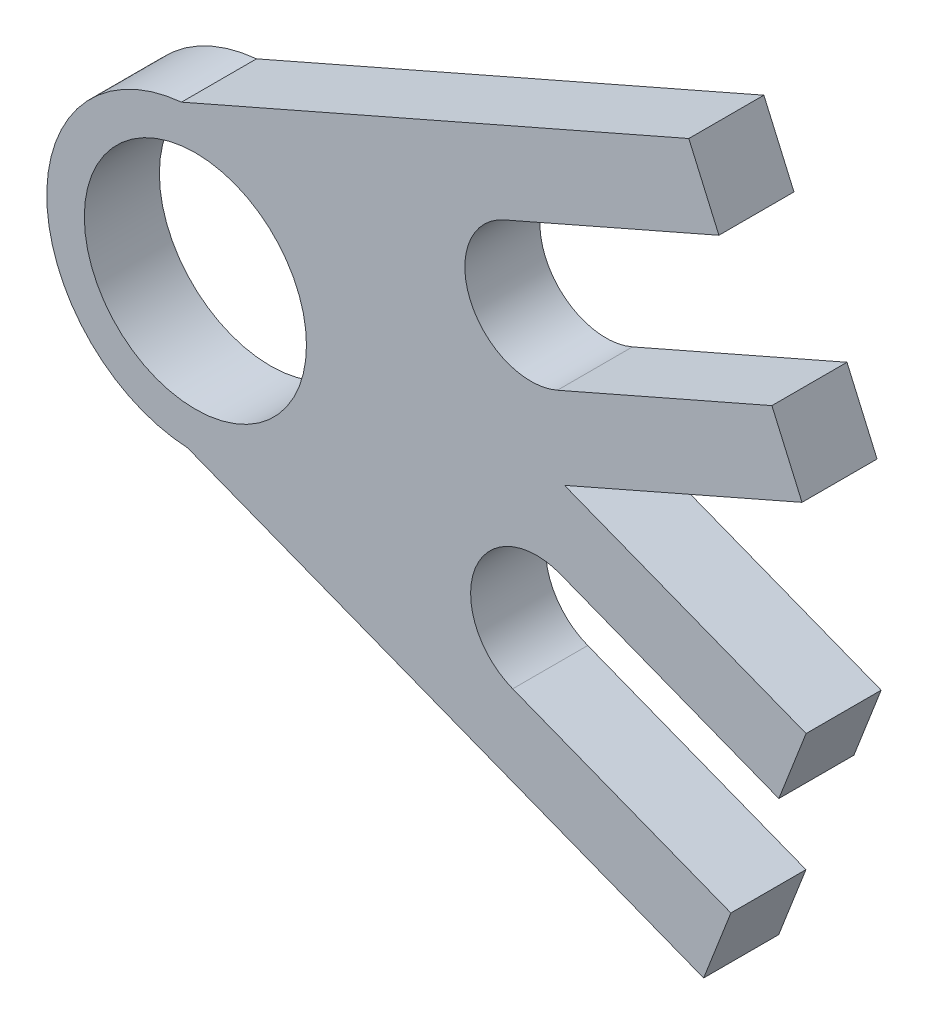
SolidWorks part; units mm, degrees
ref_plane "Front" through (0, 0, 0) normal (0, 0, 1) x (1, 0, 0)
ref_plane "Top" through (0, 0, 0) normal (0, 1, 0) x (1, 0, 0)
ref_plane "Right" through (0, 0, 0) normal (1, 0, 0) x (0, 0, -1)
sketch "Sketch1" plane through (0, 0, 0) normal (0, 0, 1) x (1, 0, 0)
  line L0 (-609.6, -8.8876) -> (-586.3332, 1.3015) construction
  line L1 (-609.6, -8.8876) -> (-241.3, 152.4) construction
  line L2 (-609.6, -8.8876) -> (-585.9333, -18.1096) construction
  line L3 (-241.3, -152.4) -> (-609.6, -8.8876) construction
  line L4 (-583.4561, 8.6618) -> (-565.3081, 16.6093)
  line L5 (-565.3081, 16.6093) -> (-567.8553, 22.426)
  line L6 (-567.8553, 22.426) -> (-610.775, 3.6304)
  line L7 (-558.2776, 0.5552) -> (-601.1973, -18.2404)
  line L8 (-560.8249, 6.3719) -> (-558.2776, 0.5552)
  line L9 (-578.9729, -1.5756) -> (-560.8249, 6.3719)
  line L10 (-582.7554, -25.3451) -> (-564.2954, -32.5383)
  line L11 (-564.2954, -32.5383) -> (-566.6009, -38.455)
  line L12 (-566.6009, -38.455) -> (-610.2584, -21.4433)
  line L13 (-557.9322, -16.2083) -> (-601.5897, 0.8034)
  line L14 (-560.2377, -22.1249) -> (-557.9322, -16.2083)
  line L15 (-578.6977, -14.9318) -> (-560.2377, -22.1249)
  circle A0 centre (-609.6, -8.8876) radius 9.398
  circle A1 centre (-609.6, -8.8876) radius 12.573
  arc A2 (-583.4561, 8.6618) -> (-578.9729, -1.5756) centre (-581.2145, 3.5431) ccw
  arc A3 (-578.6977, -14.9318) -> (-582.7554, -25.3451) centre (-580.7266, -20.1384) ccw
  point P13 (-586.3332, 1.3015)
  point P17 (-585.9333, -18.1096)
  dimension "D1" = 18.796
  dimension "D2" = 3.175
  dimension "D3" = 25.4
  dimension "D4" = 25.4
  dimension "D5" = 6.35
  dimension "D6" = 11.938
extrude "Boss-Extrude1" add sketch "Sketch1" along normal mid plane 6.35 contours A2 L4 L5 L6 A1 L13 L7 L8 L9 | A1 L7 L13 | A3 L15 L14 L13 L7 A1 L12 L11 L10 | A1 A0
move or copy body "Body-Move/Copy1" [suppressed] bodies to move or copy 101
